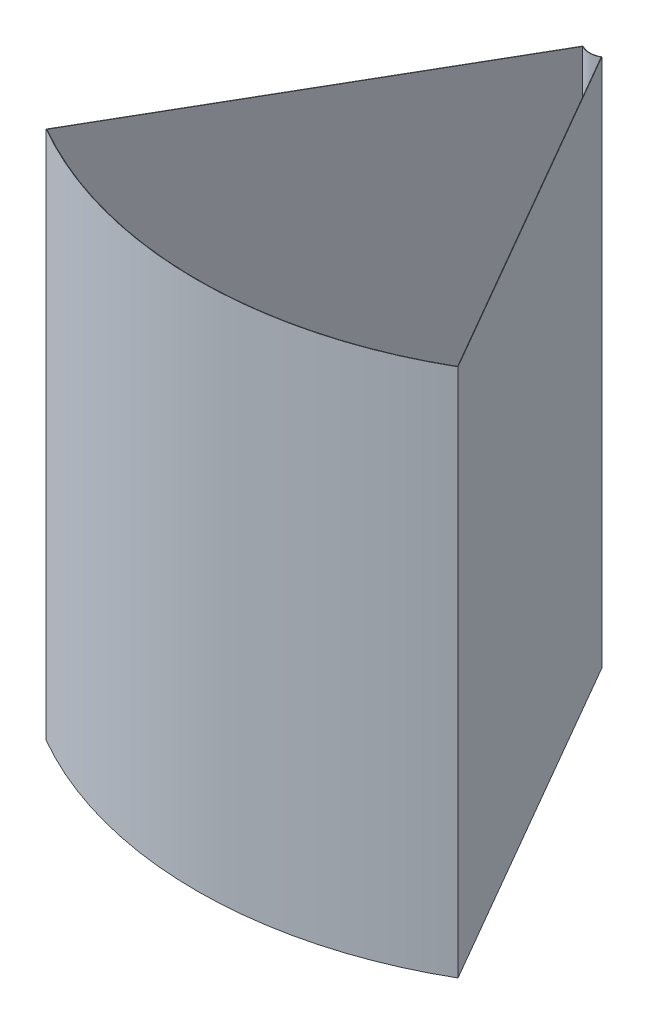
SolidWorks part; units mm, degrees
ref_plane "Front Plane" through (0, 0, 0) normal (0, 0, 1) x (1, 0, 0)
ref_plane "Top Plane" through (0, 0, 0) normal (0, 1, 0) x (1, 0, 0)
ref_plane "Right Plane" through (0, 0, 0) normal (1, 0, 0) x (0, 0, -1)
sketch "Sketch1" plane through (0, 0, 0) normal (0, 1, 0) x (1, 0, 0)
  line L2 (-8, -13.8564) -> (-175.0875, -303.2604)
  line L6 (175.0875, -303.2604) -> (8, -13.8564)
  arc A3 (-8, -13.8564) -> (8, -13.8564) centre (0, 0) ccw
  arc A4 (-175.0875, -303.2604) -> (175.0875, -303.2604) centre (0, 0) ccw
  dimension "D1" = 32
  dimension "D2" = 700.35
  dimension "D3" = 60
extrude "Boss-Extrude1" add sketch "Sketch1" along normal blind 450
shell "Shell1" thickness 0.35
